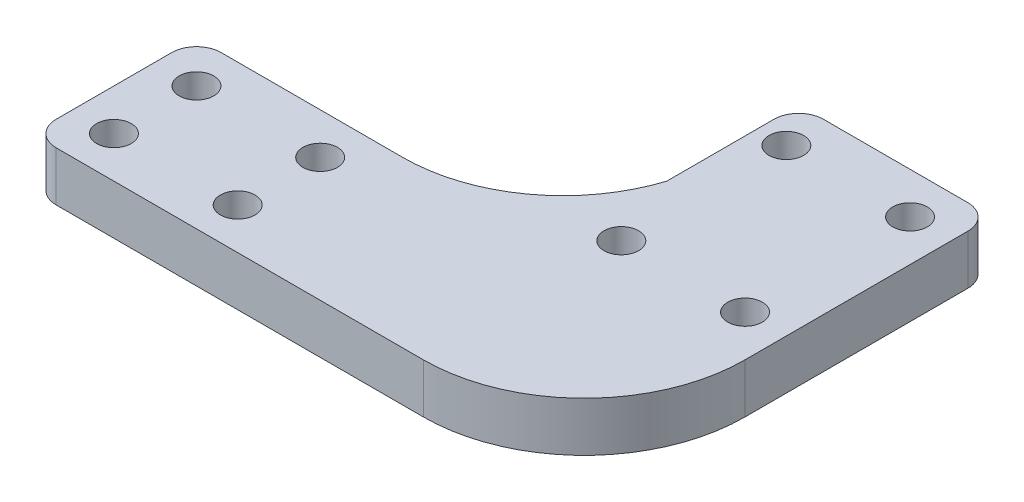
SolidWorks part; units mm, degrees
material "Thornel Mat VMA"
ref_plane "前视基准面" through (0, 0, 0) normal (0, 0, 1) x (1, 0, 0)
ref_plane "上视基准面" through (0, 0, 0) normal (0, 1, 0) x (1, 0, 0)
ref_plane "右视基准面" through (0, 0, 0) normal (1, 0, 0) x (0, 0, -1)
sketch "草图1" plane through (0, 0, 0) normal (0, 1, 0) x (1, 0, 0)
  line L1 (-7.5, 10) -> (7.5, 10) construction
  line L2 (-7.5, 10) -> (-7.5, -10) construction
  line L3 (-7.5, -10) -> (7.5, -10) construction
  line L4 (7.5, 10) -> (7.5, -10) construction
  line L5 (0, -10) -> (0, 10) construction
  line L6 (-7.5, 0) -> (7.5, 0) construction
  line L7 (-49.5, -19.5) -> (-34.5, -19.5) construction
  line L8 (-49.5, -19.5) -> (-49.5, -29.5) construction
  line L9 (-49.5, -29.5) -> (-34.5, -29.5) construction
  line L10 (-34.5, -19.5) -> (-34.5, -29.5) construction
  line L11 (-42, -29.5) -> (-42, -19.5) construction
  line L12 (-49.5, -24.5) -> (-34.5, -24.5) construction
  line L13 (-11, 15) -> (12.5, 15)
  line L14 (12.5, 15) -> (12.5, -15)
  line L16 (-7, -34.5) -> (-54.5, -34.5)
  line L17 (-54.5, -34.5) -> (-54.5, -14.5)
  line L18 (-11, 15) -> (-11, -1)
  line L21 (-54.5, -14.5) -> (-29.5, -14.5)
  circle A0 centre (-49.5, -19.5) radius 2.1
  circle A1 centre (-7.5, -10) radius 2.1
  circle A2 centre (-34.5, -19.5) radius 2.1
  circle A3 centre (-34.5, -29.5) radius 2.1
  circle A4 centre (-49.5, -29.5) radius 2.1
  circle A5 centre (7.5, -10) radius 2.1
  circle A6 centre (7.5, 10) radius 2.1
  circle A7 centre (-7.5, 10) radius 2.1
  arc A8 (-7, -34.5) -> (12.5, -15) centre (-7, -15) ccw
  arc A9 (-29.5, -14.5) -> (-11, -1) centre (-29.5, 4.9259) ccw
  point P0 (0, 0)
  point P4 (-42, -24.5)
  dimension "D5" = 4.2
  dimension "D1" = 15
  dimension "D2" = 20
  dimension "D3" = 15
  dimension "D4" = 10
  dimension "D6" = 42
  dimension "D7" = 24.5
  dimension "D8" = 5
  dimension "D9" = 5
  dimension "D10" = 5
  dimension "D11" = 5
  dimension "D13" = 3.5
  dimension "D14" = 5
  dimension "D15" = 5
  dimension "D16" = 16
  dimension "D17" = 25
extrude "凸台-拉伸1" add sketch "草图1" along normal blind 6
fillet "圆角1" radius 3 4 edges at (-11, 3, -15) (12.5, 3, -15) (-54.5, 3, 34.5) (-54.5, 3, 14.5)
